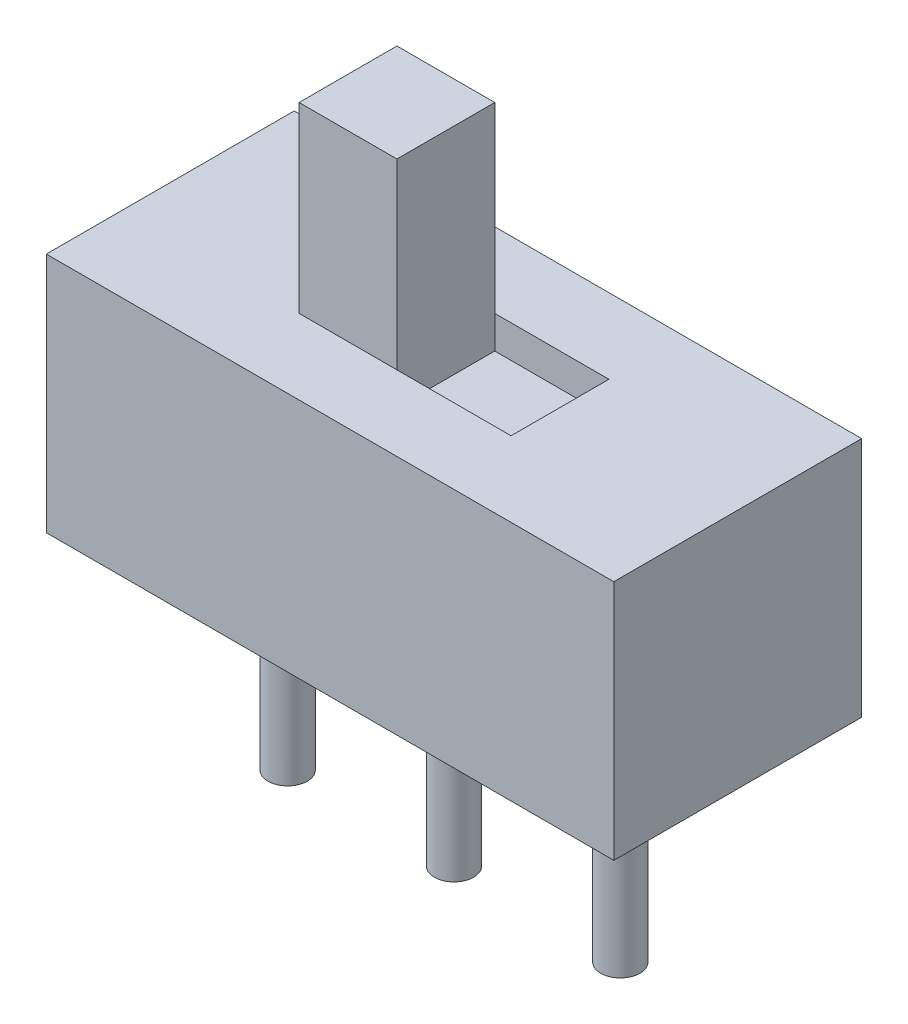
SolidWorks part; units mm, degrees
ref_plane "Plan de face" through (0, 0, 0) normal (0, 0, 1) x (1, 0, 0)
ref_plane "Plan de dessus" through (0, 0, 0) normal (0, 1, 0) x (1, 0, 0)
ref_plane "Plan de droite" through (0, 0, 0) normal (1, 0, 0) x (0, 0, -1)
sketch "Esquisse1" plane through (0, 0, 0) normal (0, 0, 1) x (1, 0, 0)
  line L1 (0, 0) -> (8.7, 0)
  line L2 (0, 0) -> (0, 3.7)
  line L3 (0, 3.7) -> (8.7, 3.7)
  line L4 (8.7, 0) -> (8.7, 3.7)
  dimension "D1" = 8.7
  dimension "D2" = 3.7
extrude "Boss.-Extru.1" add sketch "Esquisse1" along normal blind 3.8
sketch "Esquisse2" plane through (0, 3.7, 0) normal (0, 1, 0) x (1, 0, 0)
  line L1 (2.725, -2.65) -> (5.975, -2.65)
  line L2 (2.725, -2.65) -> (2.725, -1.15)
  line L3 (2.725, -1.15) -> (5.975, -1.15)
  line L4 (5.975, -2.65) -> (5.975, -1.15)
  line L5 (2.725, -2.65) -> (5.975, -1.15) construction
  line L6 (2.725, -1.15) -> (5.975, -2.65) construction
  point P0 (4.35, -1.9)
  dimension "D1" = 3.25
  dimension "D2" = 1.5
extrude "Enlèv. mat.-Extru.1" cut sketch "Esquisse2" against normal blind 0.5
sketch "Esquisse3" plane through (0, 3.2, 0) normal (0, 1, 0) x (1, 0, 0)
  line L0 (2.725, -2.65) -> (5.975, -2.65) construction
  line L1 (2.725, -1.15) -> (4.225, -1.15)
  line L2 (2.725, -1.15) -> (2.725, -2.65)
  line L3 (2.725, -2.65) -> (4.225, -2.65)
  line L4 (4.225, -1.15) -> (4.225, -2.65)
  dimension "D1" = 1.5
extrude "Boss.-Extru.2" add sketch "Esquisse3" along normal blind 3.3 separate body
sketch "Esquisse4" plane through (0, 0, 0) normal (0, -1, 0) x (1, 0, 0)
  line L0 (0, 3.8) -> (0, 0) construction
  line L1 (4.35, 3.8) -> (4.35, 0) construction
  line L2 (0, 3.8) -> (8.7, 3.8) construction
  line L3 (0, 0) -> (8.7, 0) construction
  circle A0 centre (1.8, 1.9) radius 0.3
  circle A1 centre (4.35, 1.9) radius 0.3
  circle A2 centre (6.9, 1.9) radius 0.3
  dimension "D1" = 1.8
extrude "Boss.-Extru.3" add sketch "Esquisse4" along normal blind 3.2
